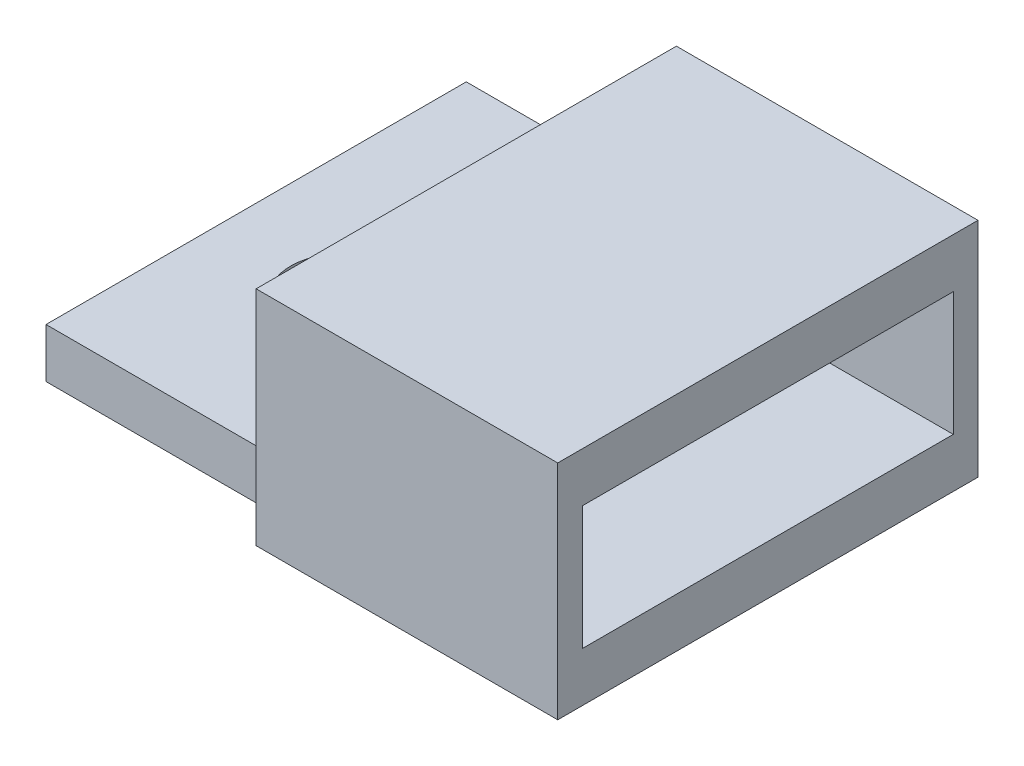
SolidWorks part; units mm, degrees
ref_plane "Front Plane" through (0, 0, 0) normal (0, 0, 1) x (1, 0, 0)
ref_plane "Top Plane" through (0, 0, 0) normal (0, 1, 0) x (1, 0, 0)
ref_plane "Right Plane" through (0, 0, 0) normal (1, 0, 0) x (0, 0, -1)
sketch "Sketch1" plane through (0, 0, 0) normal (0, 1, 0) x (1, 0, 0)
  line L0 (0, 0) -> (12, 0) construction
  line L1 (-5, -7) -> (5, -7)
  line L2 (-5, -7) -> (-5, 7)
  line L3 (-5, 7) -> (5, 7)
  line L4 (5, -7) -> (5, 7)
  line L5 (-5, -7) -> (5, 7) construction
  line L6 (-5, 7) -> (5, -7) construction
  line L8 (19, -8.5) -> (5, -8.5)
  line L9 (19, -8.5) -> (19, 8.5)
  line L10 (19, 8.5) -> (5, 8.5)
  line L11 (5, -8.5) -> (5, 8.5)
  line L12 (19, -8.5) -> (5, 8.5) construction
  line L13 (19, 8.5) -> (5, -8.5) construction
  circle A0 centre (0, 0) radius 2.1
  dimension "D1" = 4.2
  dimension "D2" = 10
  dimension "D3" = 14
  dimension "D4" = 12
  dimension "D5" = 17
extrude "Boss-Extrude1" add sketch "Sketch1" along normal blind 2 contours L1 L4 L3 L2 A0 | L11 L8 L9 L10 L4
sketch "Sketch2" plane through (0, 2, 0) normal (0, 1, 0) x (1, 0, 0)
  line L0 (19, -8.5) -> (19, 8.5) construction
  line L1 (5, -8.5) -> (19, -8.5)
  line L2 (5, -8.5) -> (5, -6.7)
  line L3 (5, -6.7) -> (19, -6.7)
  line L4 (19, -8.5) -> (19, -6.7)
  line L6 (5, 8.5) -> (19, 8.5)
  line L7 (5, 8.5) -> (5, 6.7)
  line L8 (5, 6.7) -> (19, 6.7)
  line L9 (19, 8.5) -> (19, 6.7)
  line L10 (19, 6.7) -> (17.2, 6.7)
  line L11 (19, 6.7) -> (19, -6.7)
  line L12 (19, -6.7) -> (17.2, -6.7)
  line L13 (17.2, 6.7) -> (17.2, -6.7)
  line M5 (5, -7) -> (5, -8.5)
  line M6 (5, -8.5) -> (19, -8.5)
  line M7 (19, -8.5) -> (19, 8.5)
  line M8 (19, 8.5) -> (5, 8.5)
  line M9 (5, 8.5) -> (5, 7)
  dimension "D1" = 1.8
  dimension "D2" = 1.8
  dimension "D3" = 1.8
extrude "Boss-Extrude2" add sketch "Sketch2" along normal blind 5 contours L7 L8 M7 M8 M9 | L8 L13 L3 M7 | L3 L2 M5 M6 M7
sketch "Sketch3" plane through (0, 7, 0) normal (0, 1, 0) x (1, 0, 0)
  line L1 (19, 8.5) -> (17.2, 8.5)
  line L2 (19, 8.5) -> (19, -6.7)
  line L3 (19, -6.7) -> (17.2, -6.7)
  line L4 (17.2, 8.5) -> (17.2, -6.7)
  line L5 (17.2, -6.7) -> (19, -6.7)
  line L6 (17.2, -6.7) -> (17.2, -8.5)
  line L7 (17.2, -8.5) -> (19, -8.5)
  line L8 (19, -6.7) -> (19, -8.5)
  line M3 (17.2, 6.7) -> (17.2, -6.7)
  line M6 (5, -8.5) -> (19, -8.5)
  line M7 (19, -8.5) -> (19, 8.5)
  line M8 (19, 8.5) -> (5, 8.5)
extrude "Cut-Extrude1" cut sketch "Sketch3" against normal blind 9 contours L4 L3 M8 M3 M7 | L3 L6 M6 M7
sketch "Sketch5" plane through (0, 7, 0) normal (0, 1, 0) x (1, 0, 0)
  line L0 (5, -8.5) -> (17.2, -8.5) construction
  line L1 (5, 8.5) -> (17.2, 8.5)
  line L2 (5, 8.5) -> (5, -8.5)
  line L3 (5, -8.5) -> (17.2, -8.5)
  line L4 (17.2, 8.5) -> (17.2, -8.5)
extrude "Boss-Extrude4" add sketch "Sketch5" along normal blind 2
sketch "Sketch6" plane through (5, 0, 0) normal (-1, 0, 0) x (0, 0, 1)
  line L0 (0, 7) -> (0, 2) construction
  line L1 (-7, 2) -> (7, 2)
  line L2 (-7, 2) -> (-7, 7)
  line L3 (-7, 7) -> (7, 7)
  line L4 (7, 2) -> (7, 7)
  line L5 (-7, 7) -> (-7.5, 7)
  line L6 (-7, 7) -> (-7, 2)
  line L7 (-7, 2) -> (-7.5, 2)
  line L8 (-7.5, 7) -> (-7.5, 2)
  line L10 (7, 2) -> (7.5, 2)
  line L11 (7, 2) -> (7, 7)
  line L12 (7, 7) -> (7.5, 7)
  line L13 (7.5, 2) -> (7.5, 7)
  line M9 (-7, 2) -> (-6.7, 2)
  line M10 (-6.7, 2) -> (-6.7, 7)
  line M11 (-6.7, 7) -> (6.7, 7)
  line M12 (6.7, 7) -> (6.7, 2)
  line M13 (6.7, 2) -> (7, 2)
  dimension "D1" = 0.5
  dimension "D2" = 0.5
extrude "Cut-Extrude2" cut sketch "Sketch6" against normal blind 14 contours L5 L8 L7 L2 | L3 L2 M9 M10 | L10 L13 L12 L4 | L3 L0 L1 M12 | L0 L1 M11 M10 | L4 L3 M13 M12
sketch "Sketch7" plane through (0, 0, -7) normal (0, 0, -1) x (-1, 0, 0)
  line L1 (-5, 2) -> (5, 2)
  line L2 (-5, 2) -> (-5, 0)
  line L3 (-5, 0) -> (5, 0)
  line L4 (5, 2) -> (5, 0)
extrude "Boss-Extrude5" add sketch "Sketch7" along normal blind 3
